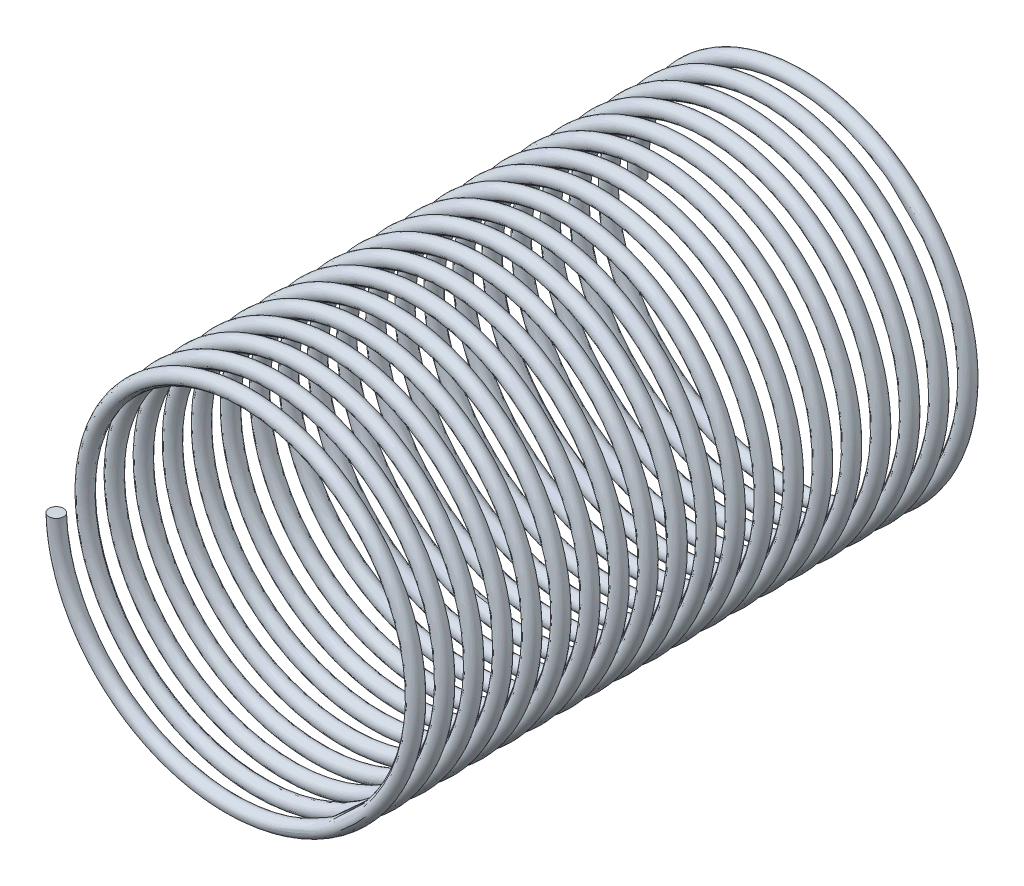
SolidWorks part; units mm, degrees
ref_plane "Front Plane" through (0, 0, 0) normal (0, 0, 1) x (1, 0, 0)
ref_plane "Top Plane" through (0, 0, 0) normal (0, 1, 0) x (1, 0, 0)
ref_plane "Right Plane" through (0, 0, 0) normal (1, 0, 0) x (0, 0, -1)
sketch "Sketch1" plane through (0, 0, 0) normal (0, 0, 1) x (1, 0, 0)
  circle A0 centre (0, 0) radius 60
curve "Helix/Spiral1" pitch 10 height 200 turns 20
sketch "Sketch4" plane through (0, 0, 0) normal (0, 1, 0) x (1, 0, 0)
  circle A0 centre (-59.2929, -0.9719) radius 2.5
sweep "Sweep1" add profiles "Sketch4" path "Helix/Spiral1"
